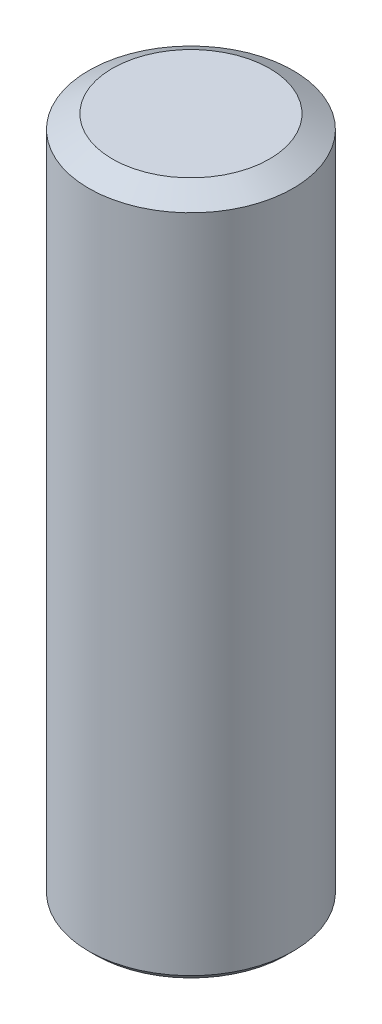
SolidWorks part; units mm, degrees
material "acero"
ref_plane "Alzado" through (0, 0, 0) normal (0, 0, 1) x (1, 0, 0)
ref_plane "Planta" through (0, 0, 0) normal (0, 1, 0) x (1, 0, 0)
ref_plane "Vista lateral" through (0, 0, 0) normal (1, 0, 0) x (0, 0, -1)
sketch "Croquis1" plane through (0, 0, 0) normal (0, 1, 0) x (1, 0, 0)
  circle A0 centre (0, 0) radius 1.5
  dimension "D1" = 3
extrude "Saliente-Extruir1" add sketch "Croquis1" along normal blind 10
sketch "Croquis2" plane through (0, 0, 0) normal (0, -1, 0) x (1, 0, 0)
  line L1 (0.433, 0.75) -> (-0.433, 0.75)
  line L2 (-0.433, 0.75) -> (-0.866, 0)
  line L3 (-0.866, 0) -> (-0.433, -0.75)
  line L4 (-0.433, -0.75) -> (0.433, -0.75)
  line L5 (0.433, -0.75) -> (0.866, 0)
  line L6 (0.866, 0) -> (0.433, 0.75)
  circle A0 centre (0, 0) radius 0.75 construction
  dimension "D1" = 1.5
extrude "Cortar-Extruir1" cut sketch "Croquis2" against normal blind 2
chamfer "Chaflán2" distance 0.1 angle 45 1 edges at (0, 0, 1.5)
chamfer "Chaflán3" distance 0.2 angle 60 1 edges at (0, 10, 1.5)
